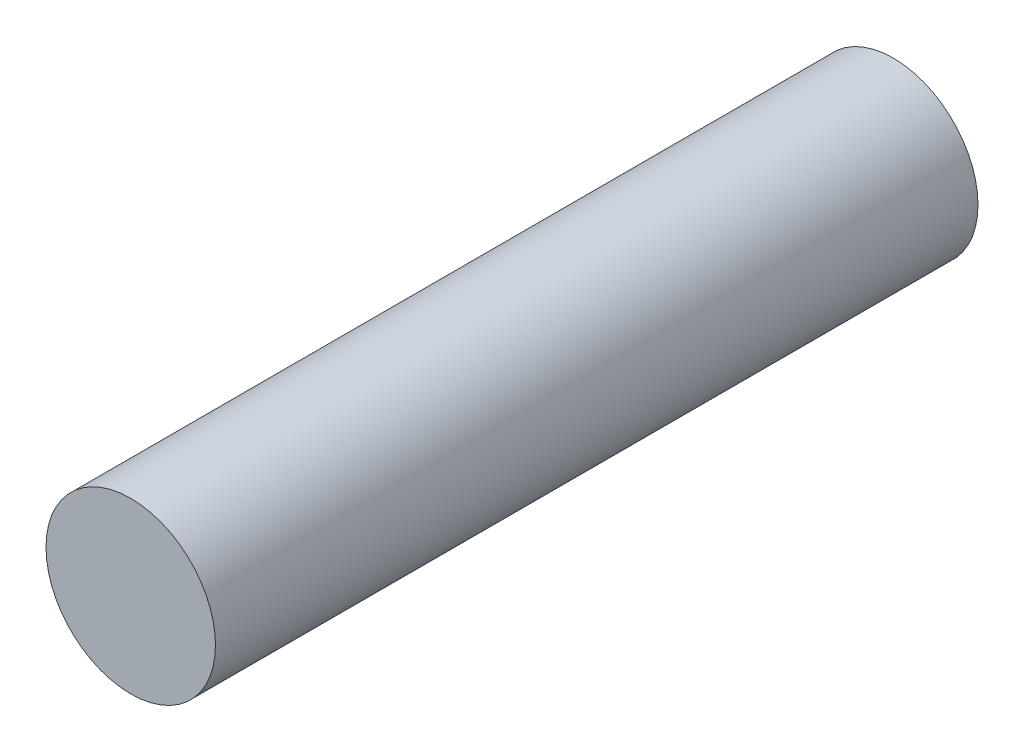
SolidWorks part; units mm, degrees
material "7079 Alloy"
ref_plane "Plane1" through (0, 0, 0) normal (0, 0, 1) x (1, 0, 0)
ref_plane "Plane2" through (0, 0, 0) normal (0, 1, 0) x (1, 0, 0)
ref_plane "Plane3" through (0, 0, 0) normal (1, 0, 0) x (0, 0, -1)
sketch "Sketch1" plane through (0, 0, 0) normal (0, 0, 1) x (1, 0, 0)
  circle A0 centre (0, 0) radius 5
  dimension "Diameter" = 10
extrude "Base-Extrude" add sketch "Sketch1" along normal blind 45
